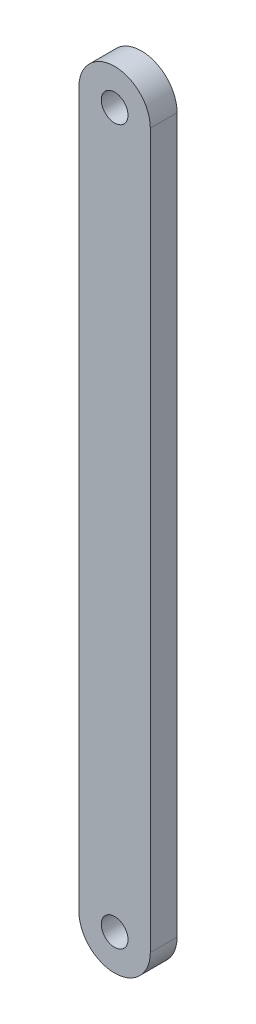
SolidWorks part; units mm, degrees
ref_plane "Front Plane" through (0, 0, 0) normal (0, 0, 1) x (1, 0, 0)
ref_plane "Top Plane" through (0, 0, 0) normal (0, 1, 0) x (1, 0, 0)
ref_plane "Right Plane" through (0, 0, 0) normal (1, 0, 0) x (0, 0, -1)
sketch "Model" plane through (0, 0, 0) normal (0, 0, 1) x (1, 0, 0)
  line L1 (47.5001, 80.0001) -> (47.5001, 0)
  line L3 (55.4999, 80.0001) -> (55.4999, 0)
  circle A0 centre (51.5001, 0) radius 1.5
  circle A1 centre (51.5001, 80) radius 1.5
  arc A2 (55.4999, 80.0001) -> (47.5001, 80.0001) centre (51.5, 80.0001) ccw
  arc A3 (47.5001, 0) -> (55.4999, 0) centre (51.5, 0) ccw
extrude "Boss-Extrude1" add sketch "Model" along normal blind 3
